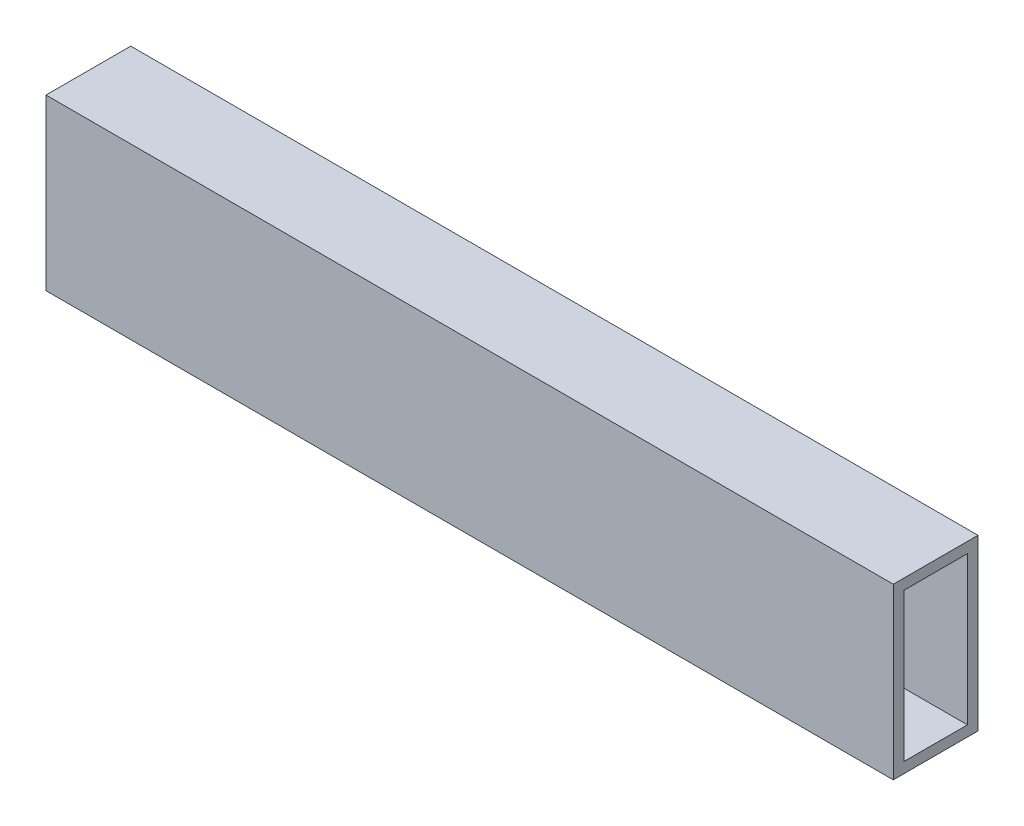
SolidWorks part; units mm, degrees
ref_plane "Front Plane" through (0, 0, 0) normal (0, 0, 1) x (1, 0, 0)
ref_plane "Top Plane" through (0, 0, 0) normal (0, 1, 0) x (1, 0, 0)
ref_plane "Right Plane" through (0, 0, 0) normal (1, 0, 0) x (0, 0, -1)
sketch "Sketch1" plane through (0, 0, 0) normal (1, 0, 0) x (0, 0, -1)
  line L1 (0, 0) -> (25.4, 0)
  line L2 (0, 0) -> (0, 50.8)
  line L3 (0, 50.8) -> (25.4, 50.8)
  line L4 (25.4, 0) -> (25.4, 50.8)
  line L5 (3.175, 47.625) -> (22.225, 47.625)
  line L6 (3.175, 47.625) -> (3.175, 3.175)
  line L7 (3.175, 3.175) -> (22.225, 3.175)
  line L8 (22.225, 47.625) -> (22.225, 3.175)
  dimension "D1" = 3.175
  dimension "D2" = 3.175
  dimension "D3" = 3.175
  dimension "D4" = 3.175
  dimension "D5" = 50.8
  dimension "D6" = 25.4
extrude "Boss-Extrude1" add sketch "Sketch1" along normal blind 254
